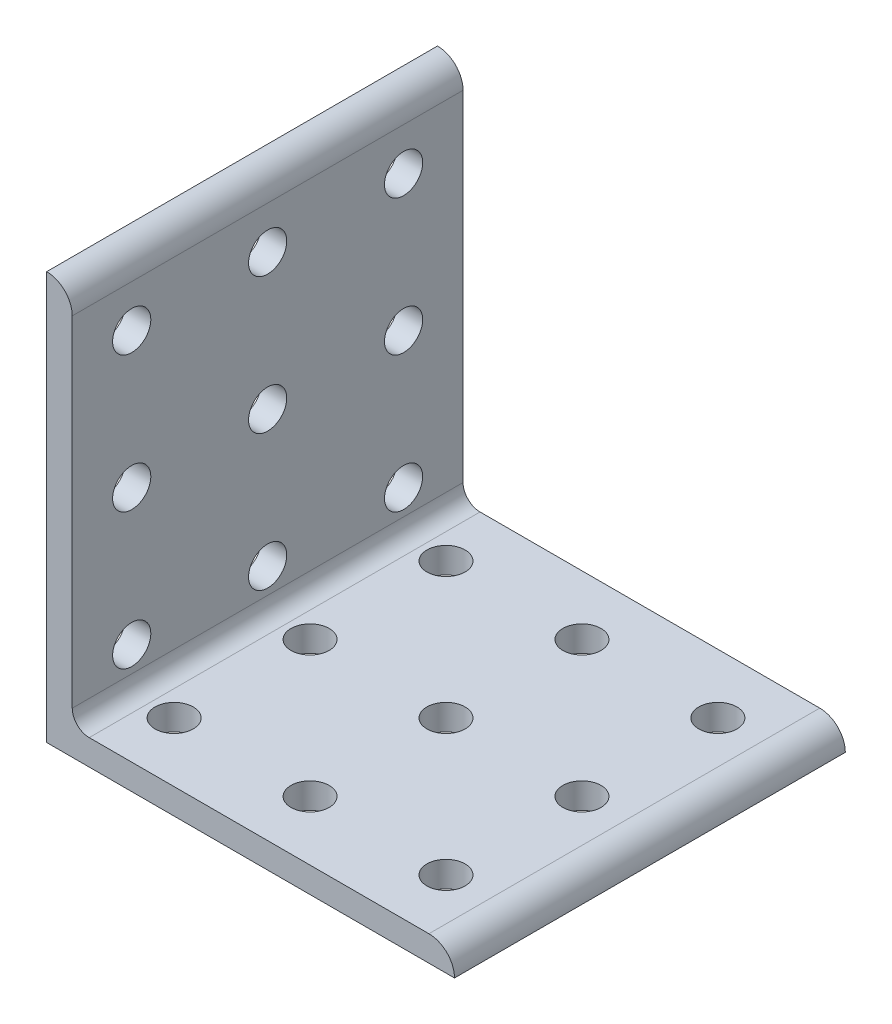
SolidWorks part; units mm, degrees
ref_plane "Front Plane" through (0, 0, 0) normal (0, 0, 1) x (1, 0, 0)
ref_plane "Top Plane" through (0, 0, 0) normal (0, 1, 0) x (1, 0, 0)
ref_plane "Right Plane" through (0, 0, 0) normal (1, 0, 0) x (0, 0, -1)
sketch "Sketch1" plane through (0, 0, 0) normal (0, 0, 1) x (1, 0, 0)
  line L0 (38.1, -38.1) -> (-38.1, -38.1) construction
  line L1 (-38.1, 38.1) -> (-38.1, -38.1) construction
  line L2 (38.1, -38.1) -> (38.1, -33.3248) construction
  point P3 (0, -38.1)
  point P6 (-38.1, 0)
  dimension "Length" = 76.2
  dimension "Thickness" = 4.7752
sketch "Sketch2" plane through (0, 0, 0) normal (1, 0, 0) x (0, 0, -1)
  line L0 (36.5125, -38.1) -> (-36.5125, -38.1) construction
  line L1 (-28.9687, -25.4) -> (-21.8313, -25.4) construction
  line L2 (0, 38.1) -> (0, -38.1) construction
  point P0 (0, -25.4)
  point P4 (0, -38.1)
  point P8 (-25.4, -25.4)
sketch "Sketch3" plane through (0, 0, 0) normal (0, 0, 1) x (1, 0, 0)
  line L0 (-38.1, 38.1) -> (-38.1, -38.1)
  line L1 (-38.1, -38.1) -> (38.1, -38.1)
  line L2 (33.3248, -33.3248) -> (-30.1498, -33.3248)
  line L3 (-33.3248, -30.1498) -> (-33.3248, 33.3248)
  arc A0 (-33.3248, 33.3248) -> (-38.1, 38.1) centre (-38.1, 33.3248) ccw
  arc A1 (33.3248, -33.3248) -> (38.1, -38.1) centre (33.3248, -38.1) cw
  arc A2 (-30.1498, -33.3248) -> (-33.3248, -30.1498) centre (-30.1498, -30.1498) cw
  dimension "Radius" = 3.175
extrude "Boss-Extrude1" add sketch "Sketch3" against normal up to vertex (36.5125 mm away) and the other way up to vertex (36.5125 mm away) up to point (0, -38.1, -36.5125) other way up to point (0, -38.1, 36.5125)
sketch "Sketch4" plane through (-33.3248, 0, 0) normal (1, 0, 0) x (0, 0, -1)
  line L0 (-28.9687, -25.4) -> (-21.8313, -25.4) construction
  line L1 (-25.4, -25.4) -> (0, -25.4) construction
  line L2 (-25.4, -25.4) -> (-25.4, 0) construction
  circle A0 centre (-25.4, -25.4) radius 3.5687
  circle A1 centre (0, -25.4) radius 3.5687
  circle A2 centre (25.4, -25.4) radius 3.5687
  circle A3 centre (0, 0) radius 3.5687
  circle A4 centre (25.4, 0) radius 3.5687
  circle A5 centre (0, 25.4) radius 3.5687
  circle A6 centre (25.4, 25.4) radius 3.5687
  circle A7 centre (-25.4, 0) radius 3.5687
  circle A8 centre (-25.4, 25.4) radius 3.5687
  dimension "D3" = 25.4
  dimension "D4" = 25.4
  dimension "D5" = 90
  dimension "D1" = 3
  dimension "D2" = 3
extrude "Cut-Extrude1" cut sketch "Sketch4" against normal through all
sketch "Sketch5" plane through (0, -33.3248, -33.3248) normal (0, 1, 0) x (1, 0, 0)
  line L1 (-25.4, -58.7248) -> (0, -58.7248) construction
  line L2 (-25.4, -58.7248) -> (-25.4, -33.3248) construction
  circle A0 centre (-25.4, -58.7248) radius 3.5687
  circle A1 centre (0, -58.7248) radius 3.5687
  circle A2 centre (25.4, -58.7248) radius 3.5687
  circle A3 centre (0, -33.3248) radius 3.5687
  circle A4 centre (25.4, -33.3248) radius 3.5687
  circle A5 centre (0, -7.9248) radius 3.5687
  circle A6 centre (25.4, -7.9248) radius 3.5687
  circle A7 centre (-25.4, -33.3248) radius 3.5687
  circle A8 centre (-25.4, -7.9248) radius 3.5687
  dimension "D3" = 25.4
  dimension "D4" = 25.4
  dimension "D5" = 90
  dimension "D1" = 3
  dimension "D2" = 3
extrude "Cut-Extrude2" cut sketch "Sketch5" against normal through all
equation "\"D4@Sketch4\"=\"Hole Spacing@Sketch2\""
equation "\"D3@Sketch4\"=\"Hole Spacing@Sketch2\""
equation "\"D4@Sketch5\"=\"Hole Spacing@Sketch2\""
equation "\"D3@Sketch5\"=\"Hole Spacing@Sketch2\""
